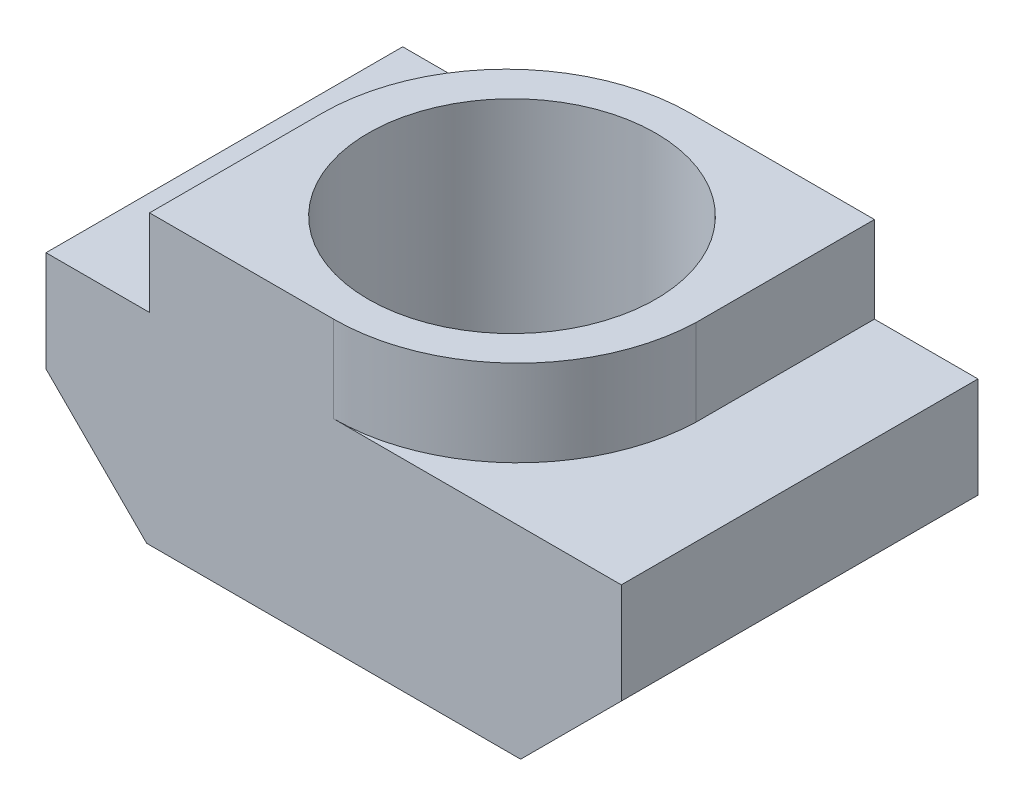
SolidWorks part; units mm, degrees
material "6061 Alloy"
ref_plane "Front Plane" through (0, 0, 0) normal (0, 0, 1) x (1, 0, 0)
ref_plane "Top Plane" through (0, 0, 0) normal (0, 1, 0) x (1, 0, 0)
ref_plane "Right Plane" through (0, 0, 0) normal (1, 0, 0) x (0, 0, -1)
sketch "Sketch1" plane through (0, 0, 0) normal (0, 0, 1) x (1, 0, 0)
  line L0 (0, 5) -> (0, 0)
  line L1 (0, -3.025) -> (0, 3.025) construction
  line L2 (0, 0) -> (3.25, 0)
  line L3 (3.41, 0) -> (-3.41, 0) construction
  line L4 (3.25, 0) -> (5, 1.75)
  line L5 (5, 1.75) -> (5, 3.5)
  line L6 (5, 3.5) -> (3.2, 3.5)
  line L7 (3.2, 3.5) -> (3.2, 5)
  line L8 (3.2, 5) -> (0, 5)
  dimension "D1" = 3.5
  dimension "D2" = 5
  dimension "D3" = 45
  dimension "D4" = 3.2
  dimension "D5" = 1.75
  dimension "D6" = 1.5
extrude "Boss-Extrude1" add sketch "Sketch1" along normal blind 6.2
mirror "Mirror1" about plane through (0, 0, 0) normal (1, 0, 0) of bodies 101
sketch "Sketch2" plane through (0, 5, 0) normal (0, 1, 0) x (1, 0, 0)
  line L0 (0, -3.025) -> (0, 3.025) construction
  line L1 (-3.025, 0) -> (3.025, 0) construction
  circle A0 centre (0, -3.1) radius 2.5
  dimension "D1" = 5
  dimension "D2" = 3.1
extrude "Cut-Extrude1" cut sketch "Sketch2" against normal blind 8 contours A0
sketch "Sketch3" plane through (0, 5, 0) normal (0, 1, 0) x (1, 0, 0)
  line L0 (3.2, -6.2) -> (-3.2, -6.2) construction
  line L2 (0, -3.025) -> (0, 3.025) construction
  line L3 (0, -6.2) -> (5.7282, -10.1248)
  line L4 (5.7282, -10.1248) -> (3.2, -3.1)
  line L5 (3.2, -6.2) -> (3.2, 0) construction
  line L6 (-3.025, 0) -> (3.025, 0) construction
  line L7 (-3.2, -3.2) -> (-7.6858, 1.6159)
  line L8 (-3.2, -6.2) -> (-3.2, 0) construction
  line L9 (-7.6858, 1.6159) -> (0, 0)
  arc A0 (0, -6.2) -> (3.2, -3.1) centre (0, -2.9984) ccw
  arc A1 (0, 0) -> (-3.2, -3.2) centre (0, -3.2) ccw
  line M6 (3.2, 0) -> (-3.2, 0)
  line M7 (-3.2, 0) -> (-3.2, -6.2)
  line M8 (-3.2, -6.2) -> (3.2, -6.2)
  line M9 (3.2, -6.2) -> (3.2, 0)
extrude "Cut-Extrude2" cut sketch "Sketch3" against normal blind 1.5 contours A0 M8 M9 | A1 M6 M7
